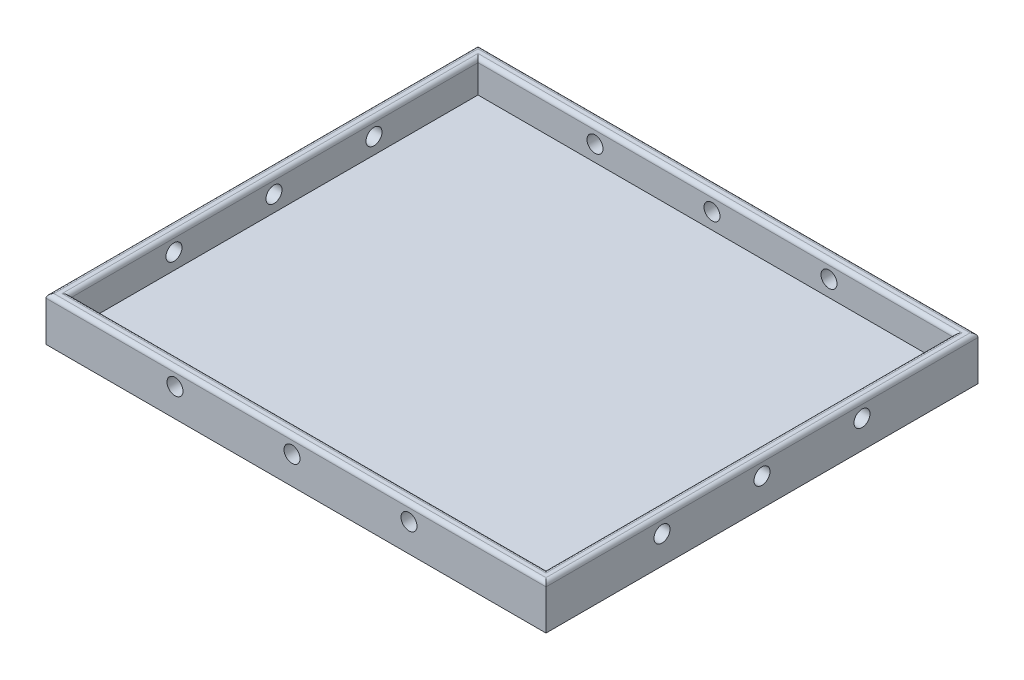
SolidWorks part; units mm, degrees
ref_plane "Front Plane" through (0, 0, 0) normal (0, 0, 1) x (1, 0, 0)
ref_plane "Top Plane" through (0, 0, 0) normal (0, 1, 0) x (1, 0, 0)
ref_plane "Right Plane" through (0, 0, 0) normal (1, 0, 0) x (0, 0, -1)
sketch "Sketch1" plane through (0, 0, 0) normal (0, 1, 0) x (1, 0, 0)
  line L1 (-201.6099, 77.8947) -> (-76.6099, 77.8947)
  line L2 (-201.6099, 77.8947) -> (-201.6099, -30.1053)
  line L3 (-201.6099, -30.1053) -> (-76.6099, -30.1053)
  line L4 (-76.6099, 77.8947) -> (-76.6099, -30.1053)
  dimension "D1" = 125
  dimension "D2" = 108
extrude "Boss-Extrude1" add sketch "Sketch1" along normal blind 11
sketch "Sketch4" plane through (0, 11, 0) normal (0, 1, 0) x (1, 0, 0)
  line L0 (-201.6099, 77.8947) -> (-201.6099, -30.1053) construction
  line L1 (-198.6099, 74.8947) -> (-79.6099, 74.8947)
  line L2 (-198.6099, 74.8947) -> (-198.6099, -27.1053)
  line L3 (-198.6099, -27.1053) -> (-79.6099, -27.1053)
  line L4 (-79.6099, 74.8947) -> (-79.6099, -27.1053)
  line L5 (-76.6099, 77.8947) -> (-201.6099, 77.8947) construction
  line L6 (-76.6099, -30.1053) -> (-76.6099, 77.8947) construction
  line L7 (-201.6099, -30.1053) -> (-76.6099, -30.1053) construction
  dimension "D1" = 3
  dimension "D2" = 3
  dimension "D3" = 3
  dimension "D4" = 3
extrude "Cut-Extrude1" cut sketch "Sketch4" against normal blind 8
sketch "Sketch5" plane through (0, 0, -74.8947) normal (0, 0, 1) x (1, 0, 0)
  line L0 (-198.6099, 3) -> (-198.6099, 11) construction
  line L1 (-79.6099, 3) -> (-198.6099, 3) construction
  circle A0 centre (-169.3599, 7) radius 2
  circle A1 centre (-140.1099, 7) radius 2
  circle A2 centre (-110.8599, 7) radius 2
  dimension "D1" = 29.25
  dimension "D2" = 29.25
  dimension "D3" = 29.25
  dimension "D4" = 4
  dimension "D5" = 4
  dimension "D6" = 4
sketch "Sketch6" plane through (-198.6099, 0, 0) normal (1, 0, 0) x (0, 0, -1)
  line L0 (-27.1053, 3) -> (-27.1053, 11) construction
  line L1 (74.8947, 3) -> (74.8947, 11) construction
  line L2 (74.8947, 3) -> (-27.1053, 3) construction
  circle A0 centre (-1.1053, 7) radius 2
  circle A1 centre (23.8947, 7) radius 2
  circle A2 centre (48.8947, 7) radius 2
  dimension "D1" = 26
  dimension "D2" = 25
  dimension "D3" = 25
  dimension "D4" = 26
  dimension "D5" = 4
extrude "Cut-Extrude6" cut sketch "Sketch6" against normal through all both and the other way through all
extrude "Cut-Extrude5" cut sketch "Sketch5" against normal through all both and the other way through all
fillet "Fillet2" radius 1 8 edges at (-139.1099, 11, 27.1053) (-139.1099, 11, 30.1053) (-76.6099, 11, -23.8947) (-79.6099, 11, -23.8947) (-198.6099, 11, -23.8947) (-139.1099, 11, -74.8947) (-201.6099, 11, -23.8947) (-139.1099, 11, -77.8947)
